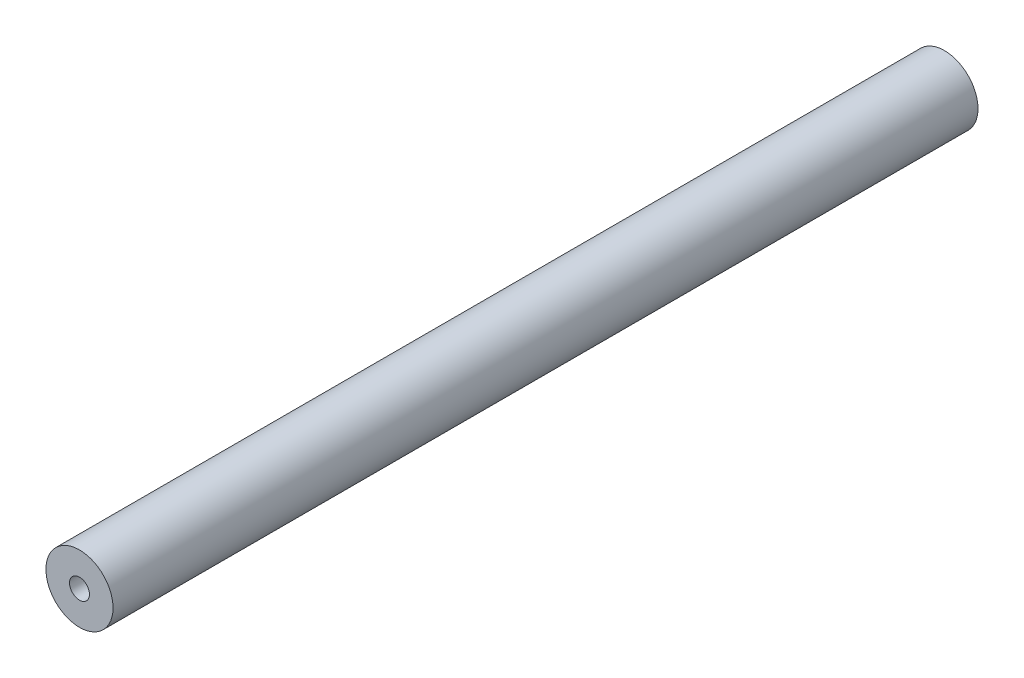
SolidWorks part; units mm, degrees
material "6061-T6 (SS)"
ref_plane "Front Plane" through (0, 0, 0) normal (0, 0, 1) x (1, 0, 0)
ref_plane "Top Plane" through (0, 0, 0) normal (0, 1, 0) x (1, 0, 0)
ref_plane "Right Plane" through (0, 0, 0) normal (1, 0, 0) x (0, 0, -1)
sketch "Sketch1" plane through (0, 0, 0) normal (0, 0, 1) x (1, 0, 0)
  circle A0 centre (0, 0) radius 6.4
  dimension "D1" = 12.8
extrude "Boss-Extrude1" add sketch "Sketch1" along normal blind 165
hole_wizard "#10-24 Tapped Hole1" positions "Sketch2" profile "Sketch3" tap size "#10-24" standard "ANSI Inch"
sketch "Sketch2" plane through (0, 0, 0) normal (0, 0, -1) x (-1, 0, 0)
  point P0 (0, 0)
sketch "Sketch3" plane through (0, 0, 0) normal (1, 0, 0) x (0, 1, 0)
  line L0 (0, 0) -> (0, 13.9708)
  line L1 (0, 13.9708) -> (1.8986, 12.83)
  line L2 (1.8986, 12.83) -> (1.8986, 0)
  line L5 (1.8986, 0) -> (0, 0)
  line L10 (0, 13.9708) -> (-1.8987, 12.83) construction
  line L11 (0, -6.35) -> (0, 107.95) construction
  dimension "Tap Drill Dia." = 3.7973
  dimension "Tap Drill Depth" = 12.83
  dimension "Drill Angle" = 118
hole_wizard "#10-24 Tapped Hole2" positions "Sketch4" profile "Sketch5" tap size "#10-24" standard "ANSI Inch"
sketch "Sketch4" plane through (0, 0, 165) normal (0, 0, 1) x (1, 0, 0)
  point P0 (0, 0)
sketch "Sketch5" plane through (0, 0, 165) normal (1, 0, 0) x (0, -1, 0)
  line L0 (0, 0) -> (0, 13.9708)
  line L1 (0, 13.9708) -> (1.8986, 12.83)
  line L2 (1.8986, 12.83) -> (1.8986, 0)
  line L5 (1.8986, 0) -> (0, 0)
  line L10 (0, 13.9708) -> (-1.8987, 12.83) construction
  line L11 (0, -6.35) -> (0, 107.95) construction
  dimension "Tap Drill Dia." = 3.7973
  dimension "Tap Drill Depth" = 12.83
  dimension "Drill Angle" = 118
